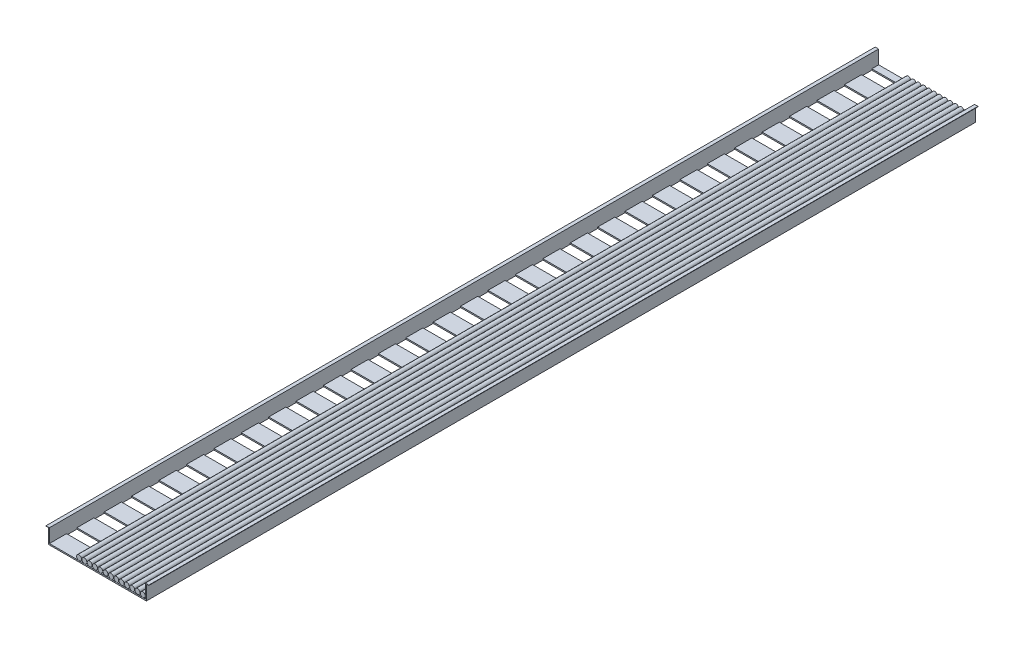
SolidWorks part; units mm, degrees
ref_plane "Alzado" through (0, 0, 0) normal (0, 0, 1) x (1, 0, 0)
ref_plane "Planta" through (0, 0, 0) normal (0, 1, 0) x (1, 0, 0)
ref_plane "Vista lateral" through (0, 0, 0) normal (1, 0, 0) x (0, 0, -1)
sketch "Croquis1" plane through (0, 0, 0) normal (0, 0, 1) x (1, 0, 0)
  line L1 (-300, -60) -> (300, -60)
  line L2 (-300, -60) -> (-300, 60)
  line L3 (-300, 60) -> (300, 60)
  line L4 (300, -60) -> (300, 60)
  line L5 (-300, -60) -> (300, 60) construction
  line L6 (-300, 60) -> (300, -60) construction
  point P0 (0, 0)
  dimension "D1" = 120
  dimension "D2" = 600
extrude "Saliente-Extruir1" add sketch "Croquis1" along normal blind 4840
sketch "Croquis2" plane through (0, 0, 4840) normal (0, 0, 1) x (1, 0, 0)
  line L0 (-280, -20) -> (-280, 60)
  line L2 (-280, -20) -> (280, -20)
  line L3 (300, 60) -> (-300, 60) construction
  line L5 (-280, 60) -> (280, 60)
  line L6 (280, 60) -> (280, -20)
  line L7 (-300, 60) -> (-300, -60) construction
  line L8 (300, -60) -> (300, 60) construction
  line L9 (-300, -60) -> (300, -60) construction
  dimension "D1" = 20
  dimension "D2" = 20
  dimension "D3" = 40
extrude "Cortar-Extruir1" cut sketch "Croquis2" against normal up to surface (4840 mm away) up to face at (0, 0, 0)
sketch "Croquis3" plane through (0, 0, 4840) normal (0, 0, 1) x (1, 0, 0)
  line L0 (-300, 58) -> (-286, 58)
  line L1 (-300, 60) -> (-300, -60) construction
  line L2 (-286, 58) -> (-286, -27.4237)
  line L3 (-286, -27.4237) -> (286, -27.4237)
  line L4 (286, -27.4237) -> (286, 58)
  line L5 (286, 58) -> (300, 58)
  line L6 (300, -60) -> (300, 60) construction
  line L7 (300, 58) -> (300, 60)
  line L8 (300, 60) -> (280, 60) construction
  line L9 (280, -20) -> (280, 60) construction
  line L10 (-280, 60) -> (-300, 60) construction
  line L11 (-280, 60) -> (-280, -20) construction
  line L12 (-300, 58) -> (-300, -60)
  line L13 (-300, -60) -> (300, -60)
  line L14 (300, -60) -> (300, 58)
  point P20 (-280, 20)
  line M10 (-300, 60) -> (-300, -60)
  line M11 (-300, -60) -> (300, -60)
  line M12 (300, -60) -> (300, 60)
  dimension "D1" = 2
  dimension "D2" = 6
  dimension "D3" = 2
  dimension "D4" = 6
extrude "Cortar-Extruir2" cut sketch "Croquis3" against normal up to surface (4840 mm away) contours L5 L4 L3 L2 L0 M10 M11 M12 up to face at (0, 10, 0)
sketch "Croquis4" plane through (0, -20, 0) normal (0, 1, 0) x (1, 0, 0)
  line L0 (-280, 0) -> (-280, -4840) construction
  line L1 (280, -4740) -> (-280, -4740)
  line L2 (280, -4740) -> (280, -4680)
  line L3 (280, -4680) -> (-280, -4680)
  line L4 (-280, -4740) -> (-280, -4680)
  line L5 (280, -4740) -> (-280, -4680) construction
  line L6 (280, -4680) -> (-280, -4740) construction
  line L7 (-280, -4840) -> (280, -4840) construction
  point P0 (0, -4710)
  dimension "D1" = 100
  dimension "D2" = 60
extrude "Cortar-Extruir3" cut sketch "Croquis4" against normal blind 4000
pattern_linear "MatrizL1" count 30 spacing 160 along (0, 0, -1) of "Cortar-Extruir3"
sketch "Croquis5" plane through (0, 0, 0) normal (0, 0, -1) x (-1, 0, 0)
  line L0 (-280, -20) -> (-280, 60) construction
  line L1 (280, -20) -> (-280, -20) construction
  circle A0 centre (-265, -5) radius 14.5
  dimension "D1" = 29
  dimension "D2" = 15
  dimension "D3" = 15
extrude "Saliente-Extruir2" add sketch "Croquis5" against normal up to surface (4840 mm away) separate body up to face at (0, 31.4294, 4840)
pattern_linear "MatrizL2" count 13 spacing 31 along (-1, 0, 0) of "Saliente-Extruir2"
